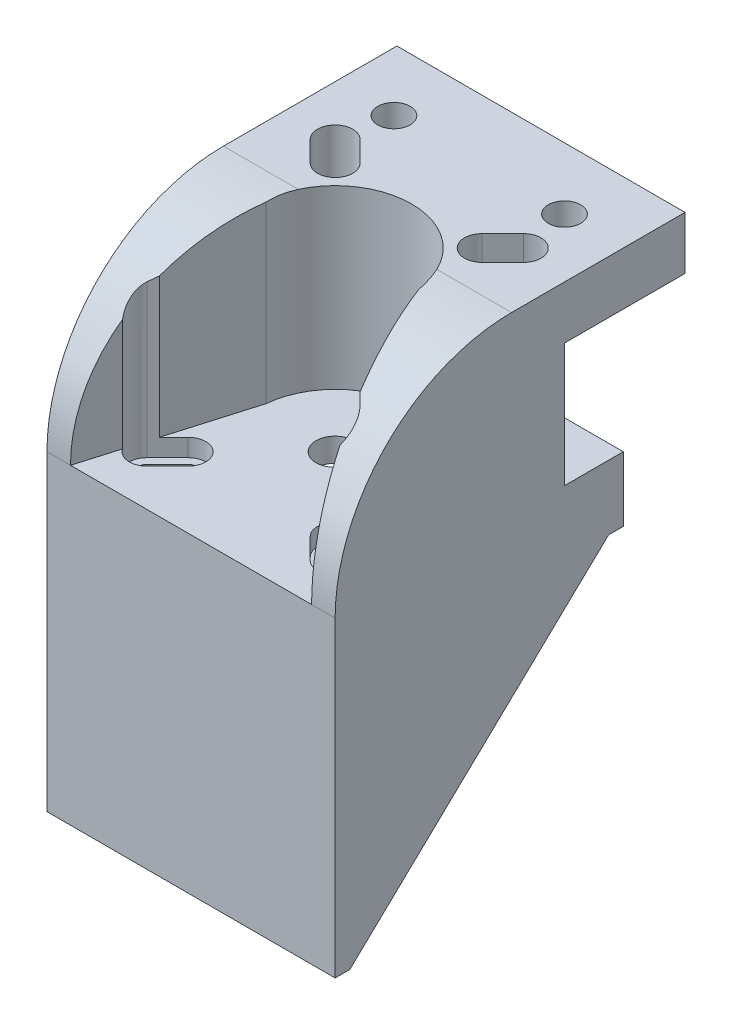
SolidWorks part; units mm, degrees
ref_plane "Front" through (0, 0, 0) normal (0, 0, 1) x (1, 0, 0)
ref_plane "Top" through (0, 0, 0) normal (0, 1, 0) x (1, 0, 0)
ref_plane "Right" through (0, 0, 0) normal (1, 0, 0) x (0, 0, -1)
sketch "Sketch1" plane through (0, 0, 0) normal (0, 1, 0) x (1, 0, 0)
  line L0 (0, 24.5) -> (0, -24.5) construction
  line L1 (-24.5, 24.5) -> (24.5, 24.5)
  line L2 (-24.5, 24.5) -> (-24.5, -24.5)
  line L3 (-24.5, -24.5) -> (24.5, -24.5)
  line L4 (24.5, 24.5) -> (24.5, -24.5)
  line L5 (24.5, 0) -> (-24.5, 0) construction
  line L6 (0, -50) -> (0, 50) construction
  line L7 (-50, 0) -> (50, 0) construction
  circle A0 centre (0, 0) radius 3.25
  point P4 (0, 24.5)
  dimension "D3" = 6.5
  dimension "D1" = 49
  dimension "D2" = 49
extrude "Boss-Extrude1" add sketch "Sketch1" along normal blind 53
sketch "Sketch2" plane through (0, 0, 0) normal (0, -1, 0) x (1, 0, 0)
  line L1 (-22, -22) -> (22, -22)
  line L2 (-22, -22) -> (-22, 22)
  line L3 (-22, 22) -> (22, 22)
  line L4 (22, -22) -> (22, 22)
  line L6 (-24.5, -24.5) -> (-24.5, 24.5) construction
  line L7 (-24.5, 24.5) -> (24.5, 24.5) construction
  point P4 (-24.5, 0)
  point P5 (0, 24.5)
  point P8 (-22, 0)
  point P11 (0, 22)
  dimension "D1" = 44
  dimension "D2" = 44
extrude "Cut-Extrude1" cut sketch "Sketch2" against normal blind 47
sketch "Sketch3" plane through (0, 47, 0) normal (0, -1, 0) x (1, 0, 0)
  circle A0 centre (0, 0) radius 13
  dimension "D1" = 26
extrude "Cut-Extrude2" cut sketch "Sketch3" against normal blind 2
sketch "Sketch4" plane through (0, 53, 0) normal (0, 1, 0) x (1, 0, 0)
  line L2 (-16, 16) -> (-12.5, 12.5) construction
  line L3 (16, 16) -> (12.5, 12.5) construction
  line L4 (12.5, -12.5) -> (16, -16) construction
  line L5 (-12.5, -12.5) -> (-16, -16) construction
  line L6 (-14.8686, 17.1314) -> (-11.3686, 13.6314)
  line L7 (-13.6314, 11.3686) -> (-17.1314, 14.8686)
  line L8 (11.3686, 13.6314) -> (14.8686, 17.1314)
  line L9 (17.1314, 14.8686) -> (13.6314, 11.3686)
  line L10 (13.6314, -11.3686) -> (17.1314, -14.8686)
  line L11 (14.8686, -17.1314) -> (11.3686, -13.6314)
  line L12 (-11.3686, -13.6314) -> (-14.8686, -17.1314)
  line L13 (-17.1314, -14.8686) -> (-13.6314, -11.3686)
  line L14 (-17.1314, -14.8686) -> (-14.8686, -17.1314) construction
  line L15 (-11.3686, -13.6314) -> (-13.6314, -11.3686) construction
  line L16 (13.6314, -11.3686) -> (11.3686, -13.6314) construction
  line L17 (14.8686, -17.1314) -> (17.1314, -14.8686) construction
  line L18 (14.8686, 17.1314) -> (17.1314, 14.8686) construction
  line L19 (13.6314, 11.3686) -> (11.3686, 13.6314) construction
  line L20 (-17.1314, 14.8686) -> (-14.8686, 17.1314) construction
  line L21 (-11.3686, 13.6314) -> (-13.6314, 11.3686) construction
  line L24 (-16, 16) -> (16, 16) construction
  line L25 (24.5, 24.5) -> (-24.5, 24.5) construction
  line L26 (-12.5, 12.5) -> (12.5, 12.5) construction
  arc A4 (-17.1314, 14.8686) -> (-14.8686, 17.1314) centre (-16, 16) cw
  arc A5 (-11.3686, 13.6314) -> (-13.6314, 11.3686) centre (-12.5, 12.5) cw
  arc A6 (14.8686, 17.1314) -> (17.1314, 14.8686) centre (16, 16) cw
  arc A7 (13.6314, 11.3686) -> (11.3686, 13.6314) centre (12.5, 12.5) cw
  arc A8 (17.1314, -14.8686) -> (14.8686, -17.1314) centre (16, -16) cw
  arc A9 (13.6314, -11.3686) -> (11.3686, -13.6314) centre (12.5, -12.5) ccw
  arc A10 (-13.6314, -11.3686) -> (-11.3686, -13.6314) centre (-12.5, -12.5) cw
  arc A11 (-17.1314, -14.8686) -> (-14.8686, -17.1314) centre (-16, -16) ccw
  point P3 (0, 16)
  point P4 (0, 12.5)
  point P36 (0, 0)
  dimension "D2" = 3.2
  dimension "D1" = 32
  dimension "D3" = 25
  dimension "D4" = 3.2
extrude "Cut-Extrude3" cut sketch "Sketch4" against normal blind 10
sketch "Sketch5" plane through (0, 53, 0) normal (0, 1, 0) x (1, 0, 0)
  line L0 (24.5, 24.5) -> (-24.5, 24.5) construction
  line L1 (-20.5, -24.5) -> (-12.9425, 1.221)
  line L2 (12.9425, 1.221) -> (-12.9425, 1.221) construction
  line L3 (24.5, 35) -> (-24.5, 35)
  line L5 (-24.5, -24.5) -> (24.5, -24.5) construction
  line L6 (-20.5, -24.5) -> (-24.5, -24.5)
  line L7 (-24.5, -24.5) -> (-24.5, 35)
  line L8 (20.5, -24.5) -> (24.5, -24.5)
  line L9 (24.5, -24.5) -> (24.5, 35)
  line L10 (24.5, -24.5) -> (24.5, 24.5) construction
  line L11 (12.9425, 1.221) -> (20.5, -24.5)
  arc A0 (0, 13) -> (12.9425, 1.221) centre (0, 0) cw
  arc A1 (0, 13) -> (-12.9425, 1.221) centre (0, 0) ccw
  dimension "D2" = 10.5
  dimension "D3" = 4
  dimension "D4" = 4
  dimension "D1" = 11.5
extrude "Boss-Extrude2" add sketch "Sketch5" along normal blind 30
sketch "Sketch7" plane through (-24.5, 0, 0) normal (-1, 0, 0) x (0, 0, 1)
  line L1 (-35, 53) -> (-14.5, 53)
  line L2 (-35, 53) -> (-35, 74)
  line L3 (-35, 74) -> (-14.5, 74)
  line L4 (-14.5, 53) -> (-14.5, 74)
  dimension "D1" = 21
  dimension "D2" = 20.5
extrude "Cut-Extrude6" cut sketch "Sketch7" against normal blind 59
sketch "Sketch9" plane through (0, 53, 0) normal (0, 1, 0) x (1, 0, 0)
  line L0 (-16, -16) -> (-12.5, -12.5) construction
  line L1 (-14.6213, 10.3787) -> (-18.1213, 13.8787)
  line L2 (-12.5, 12.5) -> (-16, 16) construction
  line L3 (12.5, 12.5) -> (16, 16) construction
  line L4 (16, -16) -> (12.5, -12.5) construction
  line L5 (-13.8787, 18.1213) -> (-10.3787, 14.6213)
  line L6 (10.3787, 14.6213) -> (13.8787, 18.1213)
  line L7 (18.1213, 13.8787) -> (14.6213, 10.3787)
  line L8 (13.8787, -18.1213) -> (10.3787, -14.6213)
  line L9 (14.6213, -10.3787) -> (18.1213, -13.8787)
  line L11 (-13.8787, -18.1213) -> (-10.3787, -14.6213)
  line L12 (-18.1213, -13.8787) -> (-14.6213, -10.3787)
  line L13 (-13.8787, -18.1213) -> (-18.1213, -13.8787) construction
  line L14 (-14.6213, -10.3787) -> (-10.3787, -14.6213) construction
  line L15 (-18.1213, 13.8787) -> (-13.8787, 18.1213) construction
  line L16 (-14.6213, 10.3787) -> (-10.3787, 14.6213) construction
  line L17 (10.3787, 14.6213) -> (14.6213, 10.3787) construction
  line L18 (13.8787, 18.1213) -> (18.1213, 13.8787) construction
  line L19 (13.8787, -18.1213) -> (18.1213, -13.8787) construction
  line L20 (14.6213, -10.3787) -> (10.3787, -14.6213) construction
  arc A0 (-13.8787, -18.1213) -> (-18.1213, -13.8787) centre (-16, -16) cw
  arc A1 (-14.6213, -10.3787) -> (-10.3787, -14.6213) centre (-12.5, -12.5) cw
  arc A2 (13.8787, -18.1213) -> (18.1213, -13.8787) centre (16, -16) ccw
  arc A4 (10.3787, -14.6213) -> (14.6213, -10.3787) centre (12.5, -12.5) cw
  arc A5 (14.6213, 10.3787) -> (10.3787, 14.6213) centre (12.5, 12.5) cw
  arc A6 (13.8787, 18.1213) -> (18.1213, 13.8787) centre (16, 16) cw
  arc A7 (-14.6213, 10.3787) -> (-10.3787, 14.6213) centre (-12.5, 12.5) ccw
  arc A8 (-18.1213, 13.8787) -> (-13.8787, 18.1213) centre (-16, 16) cw
  point P11 (-12.5, -12.5)
  point P17 (-16, -16)
  point P18 (12.5, -12.5)
  point P21 (16, -16)
  point P23 (12.5, 12.5)
  point P25 (16, 16)
  point P27 (-16, 16)
  point P29 (-12.5, 12.5)
  dimension "D1" = 6
  dimension "D3" = 6
extrude "Cut-Extrude7" cut sketch "Sketch9" along normal blind 59 and the other way blind 3
sketch "Sketch10" plane through (0, 74, 0) normal (0, -1, 0) x (1, 0, 0)
  line L0 (14.5, -24.5) -> (-14.5, -24.5) construction
  line L1 (24.5, -35) -> (-24.5, -35) construction
  line L2 (10.2639, -14.5) -> (-10.2639, -14.5) construction
  line L3 (24.5, -14.5) -> (24.5, -35) construction
  line L4 (-24.5, -14.5) -> (-24.5, -35) construction
  circle A0 centre (14.5, -24.5) radius 2.75
  circle A1 centre (-14.5, -24.5) radius 2.75
  dimension "D1" = 5.5
  dimension "D2" = 5.5
  dimension "D3" = 10
  dimension "D4" = 10
  dimension "D5" = 10
extrude "Cut-Extrude8" cut sketch "Sketch10" against normal blind 59
fillet "Fillet1" radius 30 2 edges at (22.5, 83, 24.5) (-22.5, 83, 24.5)
sketch "Sketch11" plane through (24.5, 0, 0) normal (1, 0, 0) x (0, 0, -1)
  line L0 (24.5, 0) -> (24.5, 42)
  line L1 (-22, 0) -> (22, 42)
  line L2 (-22, 0) -> (24.5, 0)
  line L3 (22, 47) -> (22, 0) construction
  line L7 (22, 42) -> (24.5, 42)
  dimension "D1" = 5
extrude "Cut-Extrude9" cut sketch "Sketch11" against normal through all
equation "\"D2@Sketch1\"=\"D1@Sketch1\""
equation "\"D2@Sketch2\"=\"D1@Sketch2\""
equation "\"D4@Sketch4\"=\"D2@Sketch4\""
equation "\"D1@Sketch5\"=\"D2@Sketch1\"/2-\"D1@Sketch3\"/2"
equation "\"D4@Sketch5\"=\"D3@Sketch5\""
equation "\"D2@Sketch5\"=20 - \"D1@Sketch5\" +2"
equation "\"D3@Sketch9\"=\"D1@Sketch9\""
equation "\"D2@Sketch10\"=\"D1@Sketch10\""
equation "\"D4@Sketch10\"=\"D3@Sketch10\""
